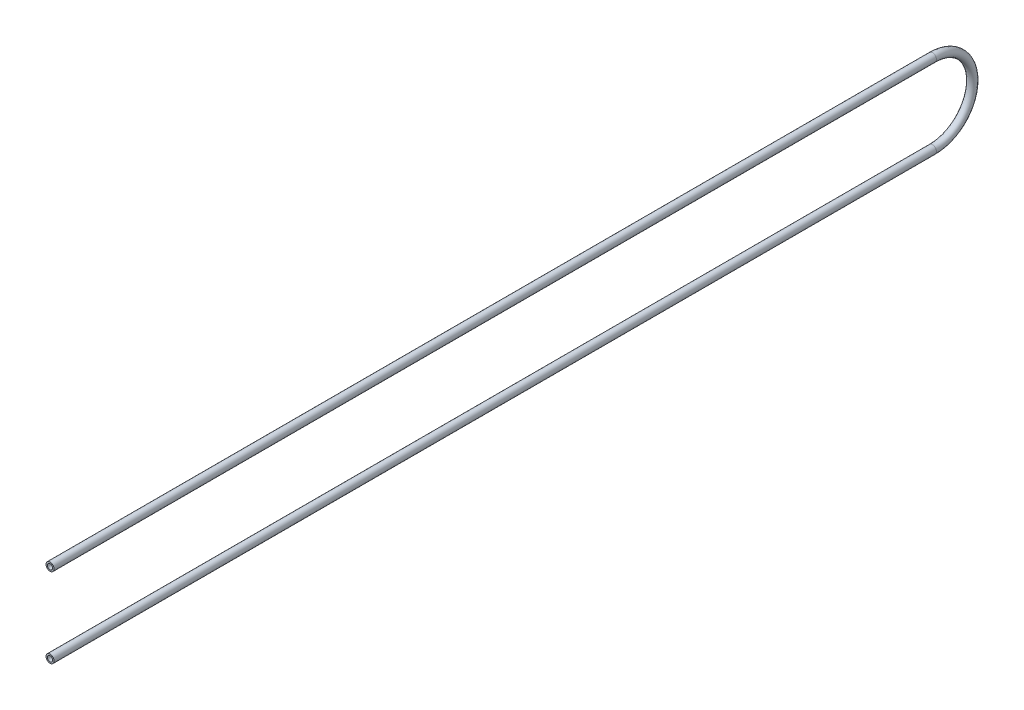
SolidWorks part; units mm, degrees
material "AISI 304"
ref_plane "Front Plane" through (0, 0, 0) normal (0, 0, 1) x (1, 0, 0)
ref_plane "Top Plane" through (0, 0, 0) normal (0, 1, 0) x (1, 0, 0)
ref_plane "Right Plane" through (0, 0, 0) normal (1, 0, 0) x (0, 0, -1)
sketch "Sketch1" plane through (0, 0, 0) normal (1, 0, 0) x (0, 0, -1)
  line L0 (0, 0) -> (0, 105) construction
  line L1 (0, 105) -> (2325, 105)
  line L2 (2325, -105) -> (0, -105)
  arc A0 (2325, 105) -> (2325, -105) centre (2325, 0) cw
  dimension "D1" = 105
  dimension "D2" = 2325
sketch "Sketch2" plane through (0, 0, 0) normal (0, 0, 1) x (1, 0, 0)
  circle A0 centre (0, 105) radius 10.65
  circle A2 centre (0, 105) radius 6.92
  dimension "D1" = 13.84
  dimension "D2" = 21.3
sweep "Sweep1" add profiles "Sketch2" path "Sketch1"
